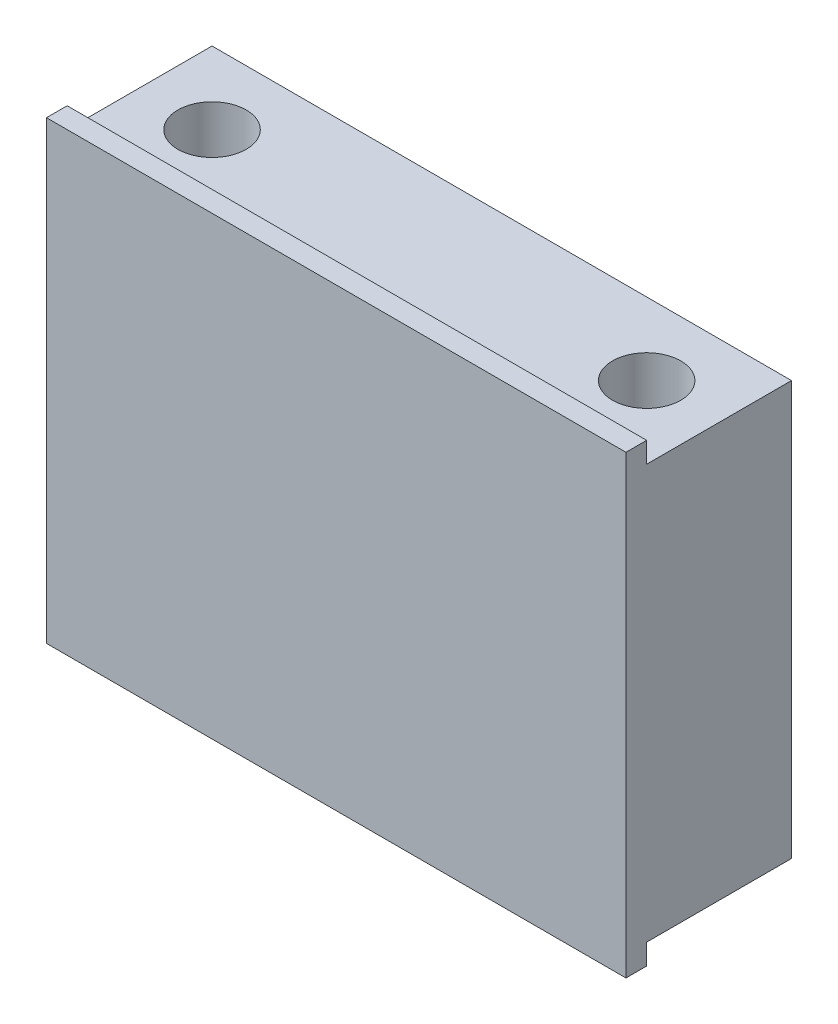
SolidWorks part; units mm, degrees
material "Polyimide"
ref_plane "Front Plane" through (0, 0, 0) normal (0, 0, 1) x (1, 0, 0)
ref_plane "Top Plane" through (0, 0, 0) normal (0, 1, 0) x (1, 0, 0)
ref_plane "Right Plane" through (0, 0, 0) normal (1, 0, 0) x (0, 0, -1)
sketch "Sketch5" plane through (0, 0, 0) normal (0, 0, 1) x (1, 0, 0)
  line L0 (-14, 10) -> (14, 10)
  line L1 (-14, 10) -> (-14, -10)
  line L2 (14, 10) -> (14, -10)
  line L3 (-14, -10) -> (14, -10)
  line L4 (-14, 0) -> (14, 0) construction
  dimension "D1" = 28
  dimension "D2" = 20
extrude "Boss-Extrude2" add sketch "Sketch5" along normal blind 4.5 and the other way blind 3.5
sketch "Sketch9" plane through (0, 10, 0) normal (0, 1, 0) x (1, 0, 0)
  line L0 (-14, -4.5) -> (14, -4.5)
  line L1 (-14, -4.5) -> (-14, -3.5)
  line L2 (14, -4.5) -> (14, -3.5)
  line L3 (-14, -3.5) -> (14, -3.5)
  dimension "D1" = 3.5
extrude "Boss-Extrude3" add sketch "Sketch9" along normal blind 1
mirror "Mirror2" about plane through (0, 0, 0) normal (0, 1, 0) of "Boss-Extrude3"
hole_wizard "M4x0.7 Tapped Hole2" positions "Sketch15" profile "Sketch14" tap size "M4x0.7" standard "Ansi Metric" end condition through all
sketch "Sketch15" plane through (0, 10, 0) normal (0, 1, 0) x (-1, 0, 0)
  line L0 (10.5, 0) -> (-10.5, 0)
  point P0 (10.5, 0)
  point P1 (-10.5, 0)
  dimension "D1" = 21
sketch "Sketch14" plane through (-10.5, 10, 0) normal (1, 0, 0) x (0, 0, 1)
  line L0 (0, 0) -> (0, 21)
  line L1 (0, 21) -> (1.65, 21)
  line L2 (1.65, 21) -> (1.65, 0)
  line L5 (1.65, 0) -> (0, 0)
  line L11 (0, -6.35) -> (0, 107.95) construction
  dimension "Thru Tap Drill Dia." = 3.3
  dimension "Thru Tap Drill Depth" = 21
cosmetic thread "Hole Thread5" parameters "D2"=4
cosmetic thread "Hole Thread6" parameters "D2"=4
sketch "Sketch17" plane through (-14, 0, 0) normal (-1, 0, 0) x (0, 0, 1)
  line L0 (2.368, -4.2952) -> (2.368, 4.3961) construction
  text T0 "TOP"
extrude "Cut-Extrude2" [suppressed] cut sketch "Sketch17" against normal blind 0.5
sketch "Sketch18" plane through (-14, 0, 0) normal (-1, 0, 0) x (0, 0, 1)
  line L0 (2.1413, -4.8965) -> (2.1413, 5.2563) construction
  text T0 "BOT"
extrude "Cut-Extrude3" cut sketch "Sketch18" against normal blind 0.5
